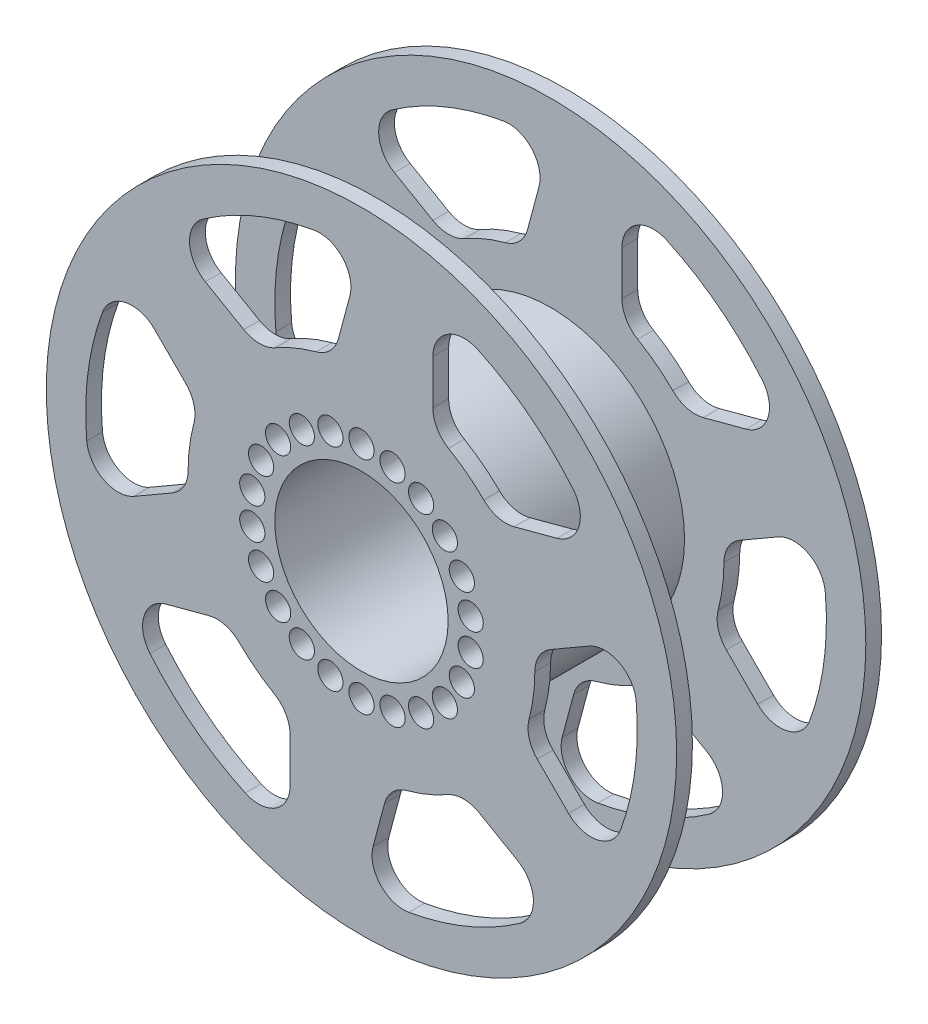
SolidWorks part; units mm, degrees
ref_plane "Plano frontal" through (0, 0, 0) normal (0, 0, 1) x (1, 0, 0)
ref_plane "Plano superior" through (0, 0, 0) normal (0, 1, 0) x (1, 0, 0)
ref_plane "Plano direito" through (0, 0, 0) normal (1, 0, 0) x (0, 0, -1)
sketch "Esboço1" plane through (0, 0, 0) normal (0, 0, 1) x (1, 0, 0)
  circle A0 centre (0, 0) radius 100
  circle A1 centre (0, 0) radius 27.5
  dimension "D1" = 200
  dimension "D2" = 55
extrude "Ressalto-extrusão1" add sketch "Esboço1" along normal blind 65
sketch "Esboço2" plane through (0, 0, 65) normal (0, 0, 1) x (1, 0, 0)
  circle A0 centre (0, 0) radius 42.5
  circle A1 centre (0, 0) radius 100 construction
  circle A2 centre (0, 0) radius 100
  dimension "D1" = 85
extrude "Corte-extrusão1" cut sketch "Esboço2" against normal blind 55 from offset 5 offset against normal yes
sketch "Esboço3" plane through (0, 0, 65) normal (0, 0, 1) x (1, 0, 0)
  line L0 (-61.8718, 61.8718) -> (-32.0828, 44.6732)
  line L1 (0, 87.5) -> (-8.9027, 54.2747)
  line L2 (0, 87.5) -> (0, 0) construction
  line L3 (-61.8718, 61.8718) -> (0, 0) construction
  circle A0 centre (0, 0) radius 55
  circle A1 centre (0, 0) radius 87.5
  dimension "D1" = 175
  dimension "D2" = 110
  dimension "D3" = 15
  dimension "D4" = 15
  dimension "D5" = 45
extrude "Corte-extrusão2" cut sketch "Esboço3" against normal blind 157.3 contours L1 A1 L0 A0
fillet "Filete1" radius 10 8 edges at (-8.9027, 54.2747, 2.5) (0, 87.5, 2.5) (-61.8718, 61.8718, 2.5) (-32.0828, 44.6732, 2.5) (-32.0828, 44.6732, 62.5) (-61.8718, 61.8718, 62.5) (-8.9027, 54.2747, 62.5) (0, 87.5, 62.5)
pattern_circular "PadrãoCircular1" count 6 every 60 about axis through (0, 0, 0) along (0, 0, 1) of "Corte-extrusão2", "Filete1"
sketch "Esboço4" plane through (0, 0, 65) normal (0, 0, 1) x (1, 0, 0)
  circle A0 centre (0, 0) radius 39
  circle A1 centre (0, 0) radius 31
  circle A2 centre (0, 35) radius 4
  dimension "D1" = 62
  dimension "D2" = 8
extrude "Corte-extrusão3" cut sketch "Esboço4" against normal blind 157.3 contours A2
pattern_circular "PadrãoCircular2" count 22 over 360 about axis through (0, 0, 0) along (0, 0, 1) of "Corte-extrusão3"
